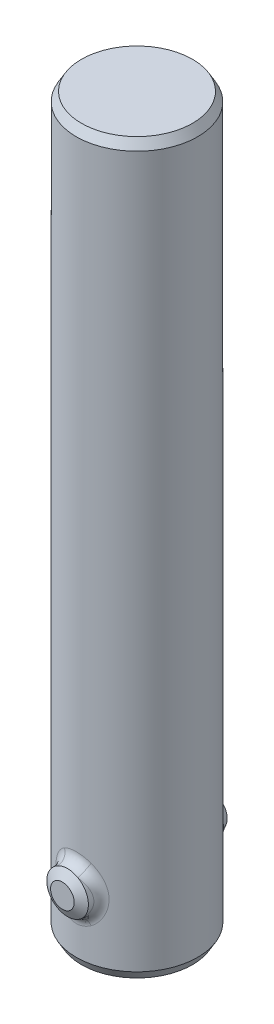
SolidWorks part; units mm, degrees
ref_plane "Front Plane" through (0, 0, 0) normal (0, 0, 1) x (1, 0, 0)
ref_plane "Top Plane" through (0, 0, 0) normal (0, 1, 0) x (1, 0, 0)
ref_plane "Right Plane" through (0, 0, 0) normal (1, 0, 0) x (0, 0, -1)
sketch "Sketch1" plane through (0, 0, 0) normal (0, 0, 1) x (1, 0, 0)
  line L0 (3.302, 0) -> (3.302, 50.8)
  line L1 (3.302, 50.8) -> (0, 50.8)
  line L2 (0, 50.8) -> (0, 53.34)
  line L3 (0, 53.34) -> (4.445, 53.34)
  line L4 (4.445, 53.34) -> (4.445, 0)
  line L5 (4.445, 0) -> (3.302, 0)
  line L6 (0, 50.8) -> (0, 0) construction
  dimension "D1" = 6.604
  dimension "D2" = 50.8
  dimension "D3" = 2.54
  dimension "D4" = 8.89
revolve "Revolve1" add sketch "Sketch1" angle 360 about L6
sketch "Sketch2" plane through (0, 0, 0) normal (0, 0, 1) x (1, 0, 0)
  line L0 (0, 0) -> (0, 5.08) construction
  circle A0 centre (0, 5.08) radius 1.524
  dimension "D1" = 3.048
  dimension "D2" = 5.08
extrude "Boss-Extrude1" add sketch "Sketch2" against normal up to next from offset 5.461
mirror "Mirror1" about plane through (0, 0, 0) normal (0, 0, 1) of "Boss-Extrude1"
chamfer "Chamfer1" distance 0.381 angle 60 5 edges at (0, 0, 4.445) (0, 0, 3.302) (0, 53.34, 4.445) (1.524, 5.08, -5.461) (1.524, 5.08, 5.461)
fillet "Fillet1" radius 0.762 2 edges at (1.5024, 4.8244, -4.1834) (-1.5024, 4.8244, 4.1834)
